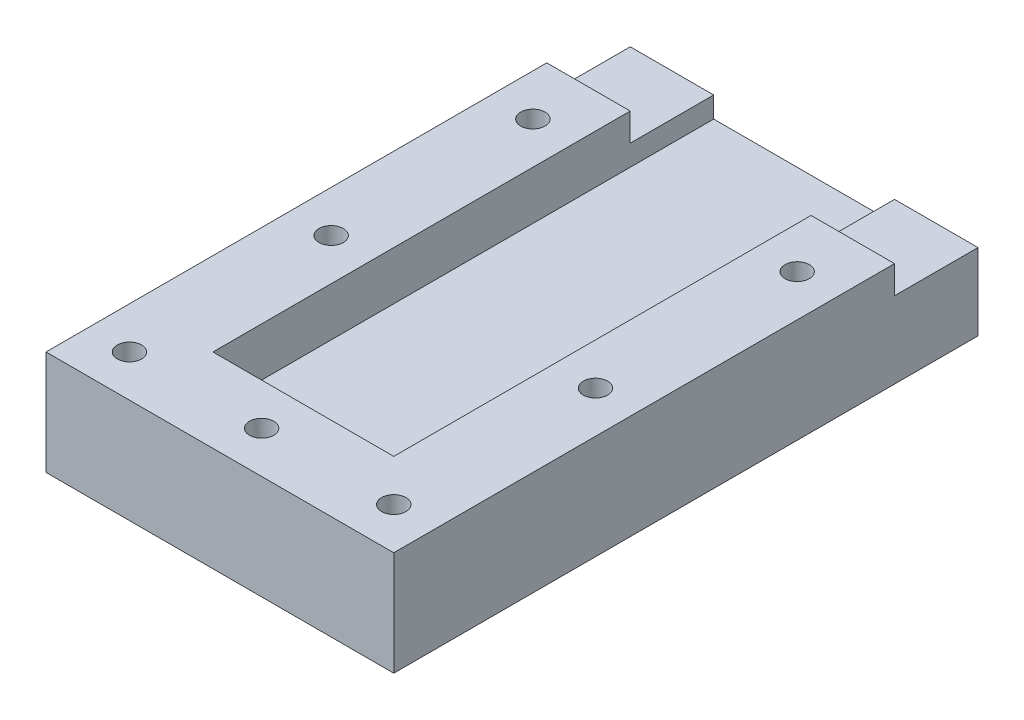
SolidWorks part; units mm, degrees
ref_plane "正面" through (0, 0, 0) normal (0, 0, 1) x (1, 0, 0)
ref_plane "平面" through (0, 0, 0) normal (0, 1, 0) x (1, 0, 0)
ref_plane "右側面" through (0, 0, 0) normal (1, 0, 0) x (0, 0, -1)
sketch "ｽｹｯﾁ1" plane through (0, 0, 0) normal (0, 0, 1) x (1, 0, 0)
  line L1 (-25, 15) -> (25, 15)
  line L2 (-25, 15) -> (-25, -15)
  line L3 (-25, -15) -> (25, -15)
  line L4 (25, 15) -> (25, -15)
  line L5 (-25, 15) -> (25, -15) construction
  line L6 (-25, -15) -> (25, 15) construction
  point P0 (0, 0)
  dimension "D1" = 30
  dimension "D2" = 50
extrude "ﾎﾞｽ - 押し出し1" add sketch "ｽｹｯﾁ1" along normal blind 84
sketch "ｽｹｯﾁ2" plane through (0, 0, 0) normal (0, 0, -1) x (-1, 0, 0)
  line L1 (13, 7) -> (-13, 7)
  line L2 (13, 7) -> (13, -7)
  line L3 (13, -7) -> (-13, -7)
  line L4 (-13, 7) -> (-13, -7)
  line L5 (13, 7) -> (-13, -7) construction
  line L6 (13, -7) -> (-13, 7) construction
  point P0 (0, 0)
  dimension "D1" = 26
  dimension "D2" = 14
extrude "ｶｯﾄ - 押し出し1" cut sketch "ｽｹｯﾁ2" against normal blind 72
ref_plane "平面1" through (0, 0, 0) normal (0, -1, 0) x (-1, 0, 0)
sketch "ｽｹｯﾁ5" plane through (13, 0, 0) normal (-1, 0, 0) x (0, 0, 1)
  line L0 (0, 7) -> (0, -7) construction
  line L1 (0, 4) -> (12, 4)
  line L2 (0, 4) -> (0, -4)
  line L3 (0, -4) -> (12, -4)
  line L4 (12, 4) -> (12, -4)
  line L6 (84, -15) -> (0, -15) construction
  dimension "D1" = 8
  dimension "D2" = 11
  dimension "D3" = 12
extrude "ｶｯﾄ - 押し出し4" cut sketch "ｽｹｯﾁ5" against normal through all
sketch "ｽｹｯﾁ6" plane through (-13, 0, 0) normal (1, 0, 0) x (0, 0, -1)
  line L0 (0, -7) -> (0, 7) construction
  line L1 (0, 4) -> (-12, 4)
  line L2 (0, 4) -> (0, -4)
  line L3 (0, -4) -> (-12, -4)
  line L4 (-12, 4) -> (-12, -4)
  line L5 (-84, -15) -> (0, -15) construction
  dimension "D1" = 12
  dimension "D2" = 8
  dimension "D3" = 11
extrude "ｶｯﾄ - 押し出し5" cut sketch "ｽｹｯﾁ6" against normal through all
sketch "ｽｹｯﾁ7" plane through (0, 15, 0) normal (0, 1, 0) x (1, 0, 0)
  line L0 (25, -84) -> (25, 0) construction
  line L1 (-25, -84) -> (-25, 0) construction
  line L2 (25, -84) -> (-25, -84) construction
  line L3 (25, 0) -> (-25, 0) construction
  circle A0 centre (19, -20) radius 1.75
  circle A1 centre (19, -49) radius 1.75
  circle A2 centre (19, -78) radius 1.75
  circle A3 centre (0, -78) radius 1.75
  circle A4 centre (-19, -78) radius 1.75
  circle A5 centre (-19, -49) radius 1.75
  circle A6 centre (-19, -20) radius 1.75
  dimension "D1" = 3.5
  dimension "D2" = 3.5
  dimension "D3" = 3.5
  dimension "D4" = 3.5
  dimension "D5" = 3.5
  dimension "D6" = 3.5
  dimension "D7" = 3.5
  dimension "D8" = 6
  dimension "D9" = 6
  dimension "D10" = 6
  dimension "D11" = 6
  dimension "D12" = 6
  dimension "D13" = 6
  dimension "D14" = 6
  dimension "D15" = 6
  dimension "D16" = 6
  dimension "D17" = 20
  dimension "D18" = 20
  dimension "D19" = 29
  dimension "D20" = 29
  dimension "D21" = 19
extrude "ｶｯﾄ - 押し出し6" cut sketch "ｽｹｯﾁ7" against normal through all
other "ｻｰﾌｪｽ ｶｯﾄ1"
